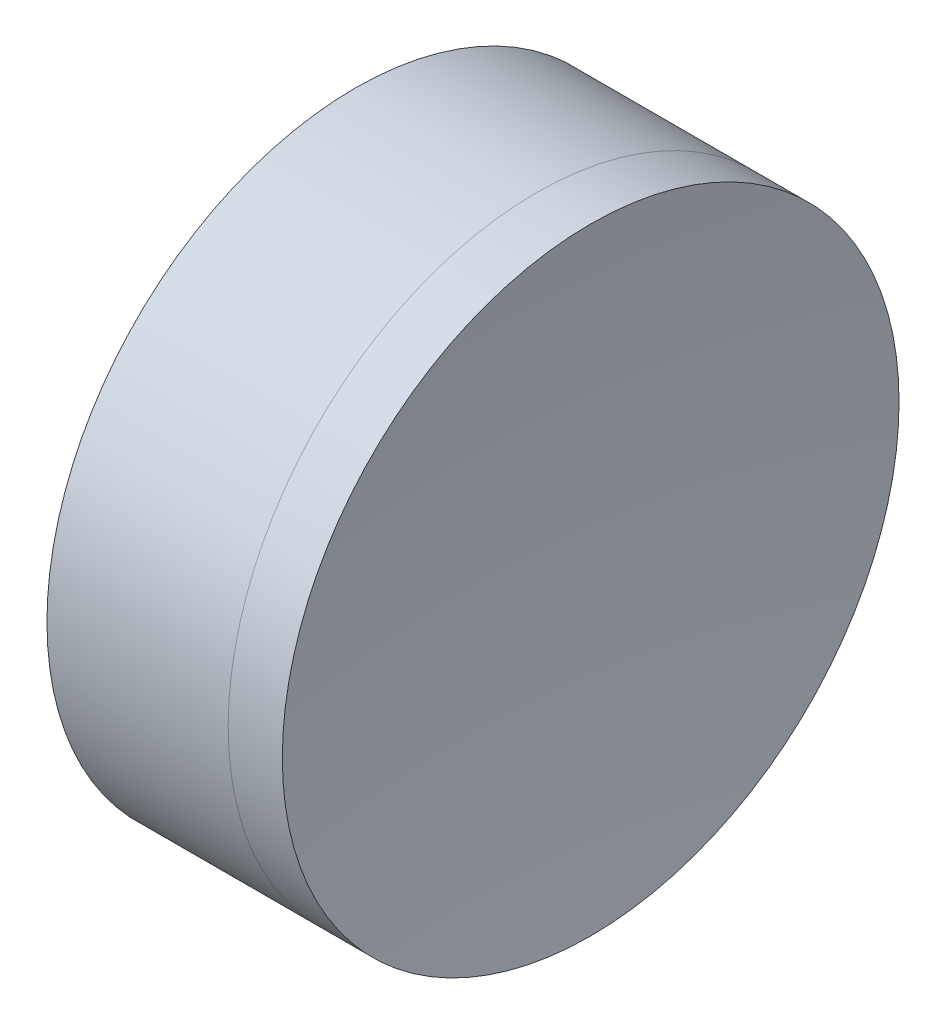
SolidWorks part; units mm, degrees
ref_plane "前视基准面" through (0, 0, 0) normal (0, 0, 1) x (1, 0, 0)
ref_plane "上视基准面" through (0, 0, 0) normal (0, 1, 0) x (1, 0, 0)
ref_plane "右视基准面" through (0, 0, 0) normal (1, 0, 0) x (0, 0, -1)
sketch "草图1" plane through (0, 0, 0) normal (0, 1, 0) x (1, 0, 0)
  line L0 (-0.8161, 0) -> (381.4836, 0) construction
  line L1 (247.1144, 20) -> (258.8681, 20)
  line L4 (247.1144, -20) -> (258.8681, -20)
  arc A0 (247.1144, -20) -> (247.1144, 20) centre (190.3338, 0) ccw
  arc A1 (258.8681, 20) -> (258.8681, -20) centre (302.8438, 0) ccw
  point P6 (250.5338, 0)
  point P8 (254.5338, 0)
  dimension "D3" = 20
  dimension "D4" = 4
  dimension "D1" = 60.2
  dimension "D5" = 48.31
  dimension "D2" = 20
revolve "旋转1" add sketch "草图1" angle 360 about L0
sketch "草图2" plane through (0, 0, 0) normal (0, 1, 0) x (1, 0, 0)
  line L2 (247.1144, 0) -> (272.9951, 0) construction
  line L3 (247.1144, -20) -> (247.1144, 20) construction
  line L6 (258.8681, 20) -> (262.3822, 20)
  line L7 (258.8681, -20) -> (262.3822, -20)
  arc A2 (258.8681, 20) -> (258.8681, -20) centre (302.8438, 0) ccw construction
  arc A3 (258.8681, 20) -> (258.8681, -20) centre (302.8438, 0) ccw
  arc A4 (262.3822, 20) -> (262.3822, -20) centre (410.0338, 0) ccw
  point P8 (254.5338, 0)
  point P9 (261.0338, 0)
  dimension "D1" = 6.5
  dimension "D2" = 149
revolve "旋转3" add sketch "草图2" angle 360 about L2
